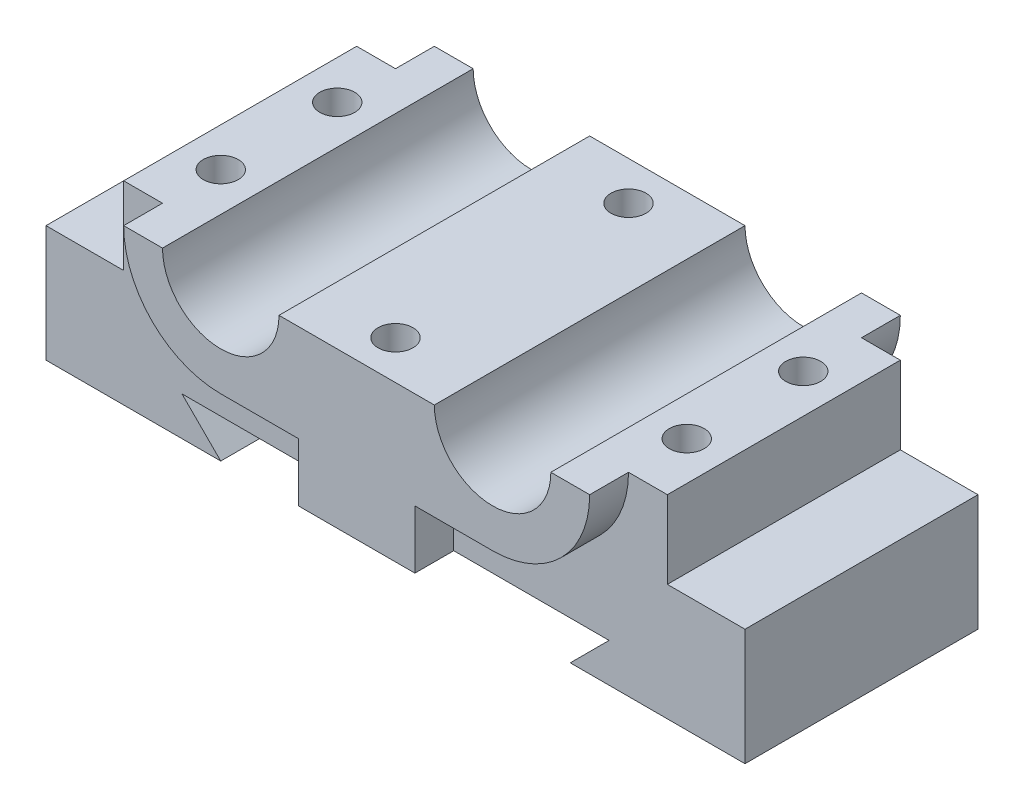
SolidWorks part; units mm, degrees
ref_plane "Front Plane" through (0, 0, 0) normal (0, 0, 1) x (1, 0, 0)
ref_plane "Top Plane" through (0, 0, 0) normal (0, 1, 0) x (1, 0, 0)
ref_plane "Right Plane" through (0, 0, 0) normal (1, 0, 0) x (0, 0, -1)
sketch "Sketch1" plane through (0, 0, 0) normal (0, 0, 1) x (1, 0, 0)
  line L0 (0, 0) -> (22.5, 0)
  line L1 (22.5, 0) -> (17.5, 5)
  line L2 (17.5, 5) -> (72.5, 5)
  line L3 (72.5, 5) -> (67.5, 0)
  line L4 (67.5, 0) -> (90, 0)
  line L5 (90, 0) -> (90, 15)
  line L6 (90, 15) -> (80, 15)
  line L7 (80, 15) -> (80, 25)
  line L8 (80, 25) -> (70, 25)
  line L9 (10, 25) -> (10, 15)
  line L10 (10, 15) -> (0, 15)
  line L11 (0, 15) -> (0, 0)
  line L12 (45, -25.7718) -> (45, 91.3336) construction
  line L13 (20, 25) -> (10, 25)
  line L14 (55, 25) -> (35, 25)
  arc A0 (20, 25) -> (35, 25) centre (27.5, 25) ccw
  arc A1 (55, 25) -> (70, 25) centre (62.5, 25) ccw
  dimension "D8" = 17.5
  dimension "D9" = 15
  dimension "D1" = 45
  dimension "D2" = 5
  dimension "D3" = 5
  dimension "D4" = 22.5
  dimension "D5" = 15
  dimension "D6" = 17.5
  dimension "D7" = 10
  dimension "D10" = 35
extrude "Boss-Extrude1" add sketch "Sketch1" along normal mid plane 40
sketch "Sketch2" plane through (0, 0, 20) normal (0, 0, 1) x (1, 0, 0)
  line L0 (45, 47.8212) -> (45, 5) construction
  line L1 (0, 15) -> (0, 0) construction
  line L2 (90, 0) -> (90, 15) construction
  line L4 (17.5, 5) -> (72.5, 5) construction
  line L5 (22.5, 0) -> (17.5, 5) construction
  line L6 (0, 0) -> (22.5, 0) construction
  line L7 (10, 15) -> (0, 15) construction
  line L8 (10, 25) -> (10, 15) construction
  line L9 (20, 25) -> (10, 25) construction
  line L10 (72.5, 5) -> (67.5, 0) construction
  line L11 (17.5, 5) -> (37.5, 5)
  line L12 (22.5, 0) -> (17.5, 5)
  line L13 (0, 0) -> (22.5, 0)
  line L14 (0, 15) -> (0, 0)
  line L15 (10, 15) -> (0, 15)
  line L16 (10, 25) -> (10, 15)
  line L17 (15, 25) -> (10, 25)
  line L18 (27.5, 12.5) -> (37.5, 12.5)
  line L19 (37.5, 5) -> (37.5, 12.5)
  line L20 (62.5, 12.5) -> (52.5, 12.5)
  line L21 (52.5, 5) -> (52.5, 12.5)
  line L22 (67.5, 0) -> (90, 0) construction
  line L23 (90, 15) -> (80, 15) construction
  line L24 (80, 15) -> (80, 25) construction
  line L25 (80, 25) -> (70, 25) construction
  line L26 (72.5, 5) -> (67.5, 0)
  line L27 (67.5, 0) -> (90, 0)
  line L28 (90, 0) -> (90, 15)
  line L29 (90, 15) -> (80, 15)
  line L30 (80, 15) -> (80, 25)
  line L31 (80, 25) -> (75, 25)
  line L32 (52.5, 5) -> (72.5, 5)
  arc A0 (15, 25) -> (27.5, 12.5) centre (27.5, 25) ccw
  arc A1 (75, 25) -> (62.5, 12.5) centre (62.5, 25) cw
  dimension "D1" = 25
  dimension "D2" = 15
extrude "Cut-Extrude1" cut sketch "Sketch2" against normal blind 5
mirror "Mirror1" about plane through (0, 0, 0) normal (0, 0, 1) of "Cut-Extrude1"
sketch "Sketch3" plane through (0, 25, 0) normal (0, 1, 0) x (1, 0, 0)
  line L0 (55, 20) -> (35, 20) construction
  line L1 (15, -15) -> (10, -15) construction
  line L2 (80, -15) -> (75, -15) construction
  circle A0 centre (45, 15) radius 2.25
  circle A1 centre (45, -15) radius 2.25
  circle A3 centre (75, 7.5) radius 2.25
  circle A4 centre (75, -7.5) radius 2.25
  circle A5 centre (15, 7.5) radius 2.25
  circle A6 centre (15, -7.5) radius 2.25
  point P4 (0, 0)
  point P15 (45, 20)
  point P18 (0, 0)
  point P19 (0, 0)
  point P20 (0, 0)
  point P21 (0, 0)
  point P22 (0, 0)
  point P23 (0, 0)
  dimension "D1" = 7.5
  dimension "D5" = 4.5
  dimension "D2" = 15
  dimension "D3" = 30
  dimension "D4" = 30
  dimension "D6" = 30
extrude "Cut-Extrude2" cut sketch "Sketch3" against normal blind 15
